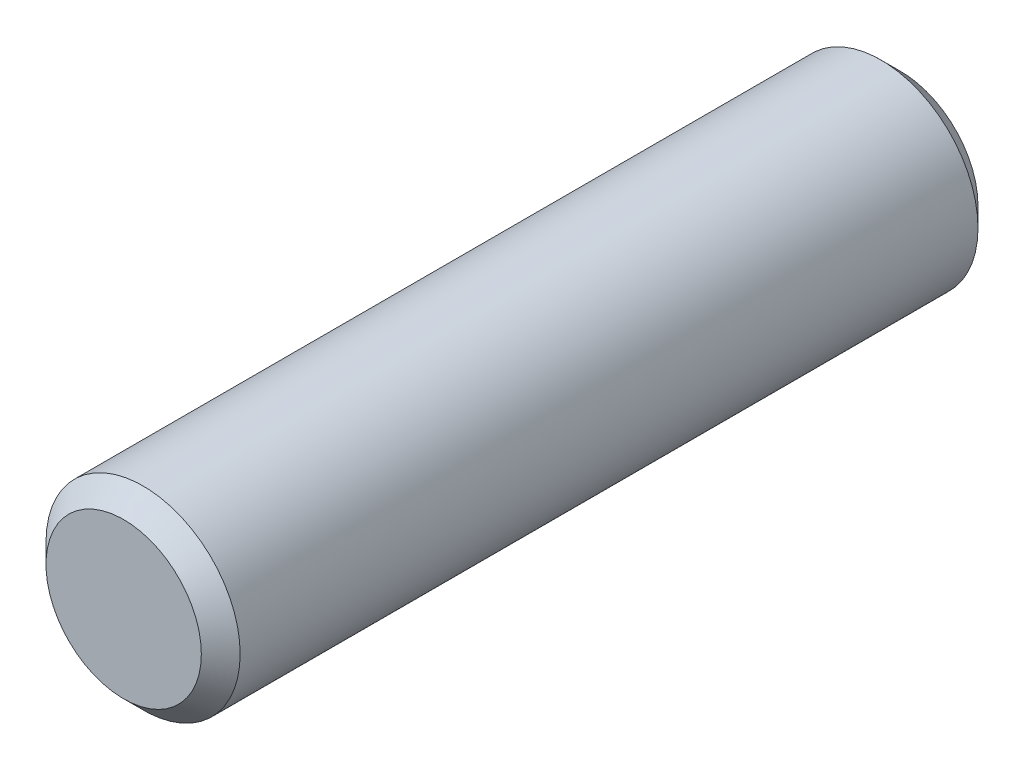
SolidWorks part; units mm, degrees
material "AISI 316 Annealed Stainless Steel Bar (SS)"
ref_plane "Front Plane" through (0, 0, 0) normal (0, 0, 1) x (1, 0, 0)
ref_plane "Top Plane" through (0, 0, 0) normal (0, 1, 0) x (1, 0, 0)
ref_plane "Right Plane" through (0, 0, 0) normal (1, 0, 0) x (0, 0, -1)
sketch "Sketch1" plane through (0, 0, 0) normal (0, 0, 1) x (1, 0, 0)
  circle A0 centre (0, 0) radius 1.5
  dimension "D1" = 3
extrude "Boss-Extrude1" add sketch "Sketch1" along normal mid plane 12
chamfer "Chamfer1" distance 0.3 angle 45 2 edges at (1.5, 0, 6) (1.5, 0, -6)
